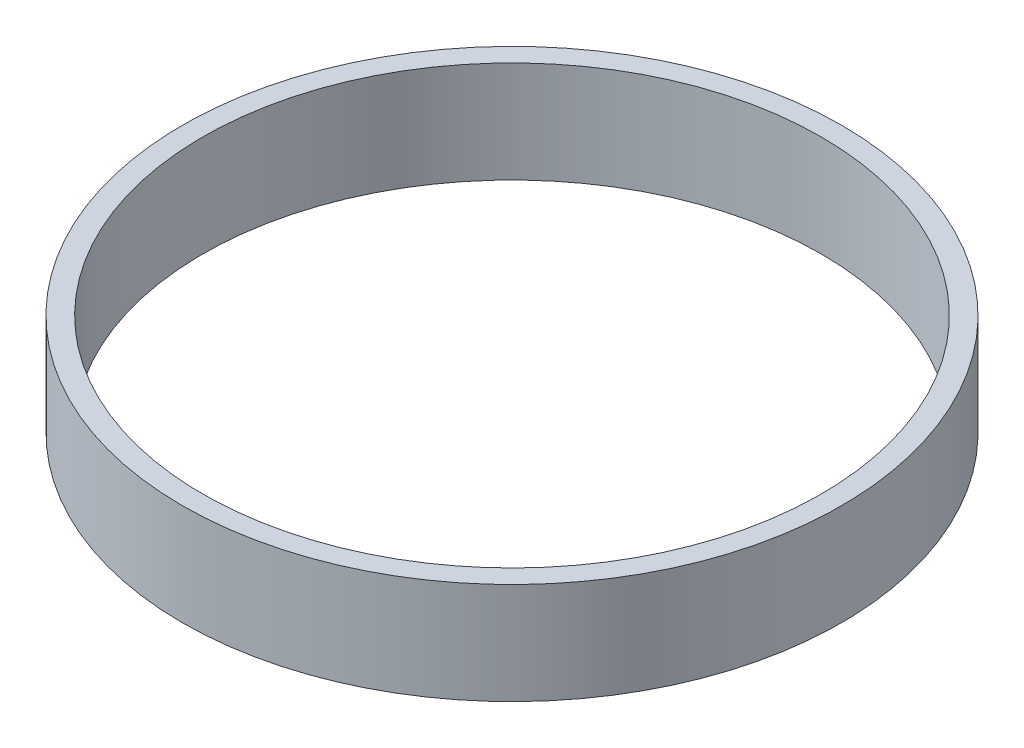
SolidWorks part; units mm, degrees
ref_plane "Plano frontal" through (0, 0, 0) normal (0, 0, 1) x (1, 0, 0)
ref_plane "Plano superior" through (0, 0, 0) normal (0, 1, 0) x (1, 0, 0)
ref_plane "Plano direito" through (0, 0, 0) normal (1, 0, 0) x (0, 0, -1)
sketch "Esboço1" plane through (0, 0, 0) normal (0, 0, 1) x (1, 0, 0)
  line L1 (30.5, 0) -> (32.5, 0)
  line L2 (32.5, 0) -> (32.5, 10)
  line L3 (32.5, 10) -> (30.5, 10)
  line L4 (30.5, 10) -> (30.5, 0)
ref_axis "Eixo1" through (0, -0.5, 0) along (0, 1, 0)
revolve "Revolução1" add sketch "Esboço1" angle 360 about axis through (0, -0.5, 0) along (0, 1, 0)
